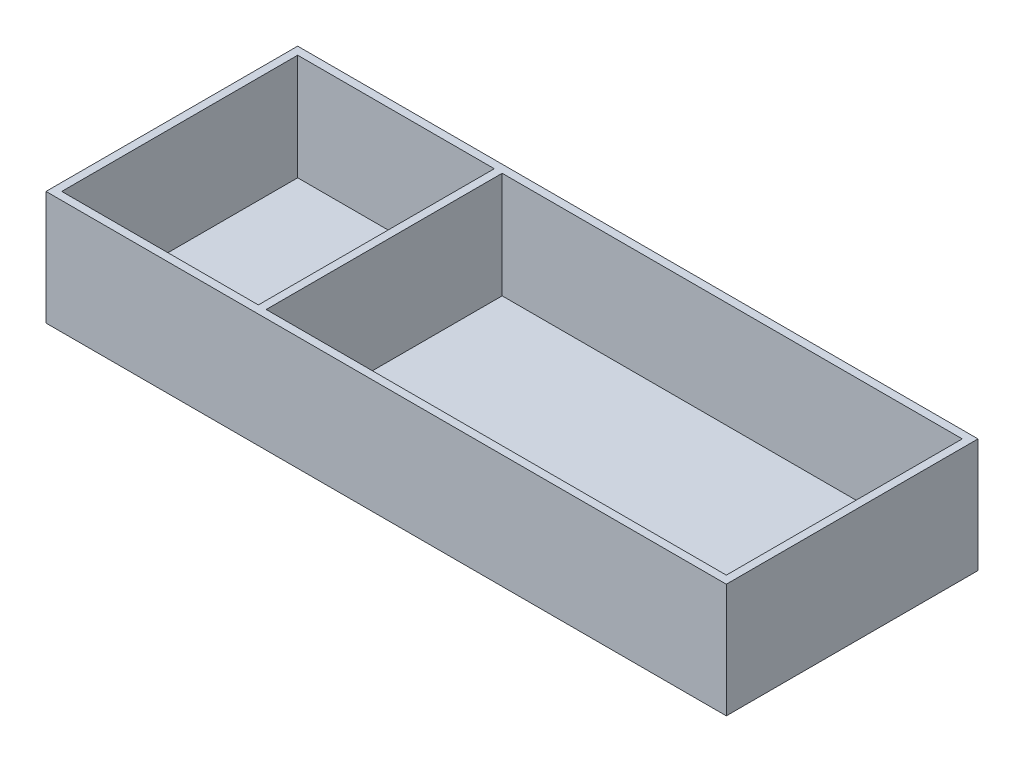
SolidWorks part; units mm, degrees
ref_plane "Front" through (0, 0, 0) normal (0, 0, 1) x (1, 0, 0)
ref_plane "Top" through (0, 0, 0) normal (0, 1, 0) x (1, 0, 0)
ref_plane "Right" through (0, 0, 0) normal (1, 0, 0) x (0, 0, -1)
sketch "Sketch1" plane through (0, 0, 0) normal (0, 1, 0) x (1, 0, 0)
  line L1 (-86.5, -32) -> (86.5, -32)
  line L2 (-86.5, -32) -> (-86.5, 32)
  line L3 (-86.5, 32) -> (86.5, 32)
  line L4 (86.5, -32) -> (86.5, 32)
  line L5 (-86.5, -32) -> (86.5, 32) construction
  line L6 (-86.5, 32) -> (86.5, -32) construction
  point P0 (0, 0)
  dimension "D1" = 64
  dimension "D2" = 173
extrude "Boss-Extrude1" add sketch "Sketch1" along normal blind 29
shell "Shell1" thickness 2
sketch "Sketch3" plane through (0, 2, 0) normal (0, 1, 0) x (1, 0, 0)
  line L0 (84.5, 30) -> (-84.5, 30) construction
  line L1 (-34.5, -30) -> (-32.5, -30)
  line L2 (-34.5, -30) -> (-34.5, 30)
  line L3 (-34.5, 30) -> (-32.5, 30)
  line L4 (-32.5, -30) -> (-32.5, 30)
  line L5 (-34.5, -30) -> (-32.5, 30) construction
  line L6 (-34.5, 30) -> (-32.5, -30) construction
  line L8 (84.5, -30) -> (84.5, 30) construction
  point P0 (-33.5, 0)
  dimension "D1" = 2
  dimension "D2" = 117
extrude "Boss-Extrude2" add sketch "Sketch3" along normal up to vertex (27 mm away)
